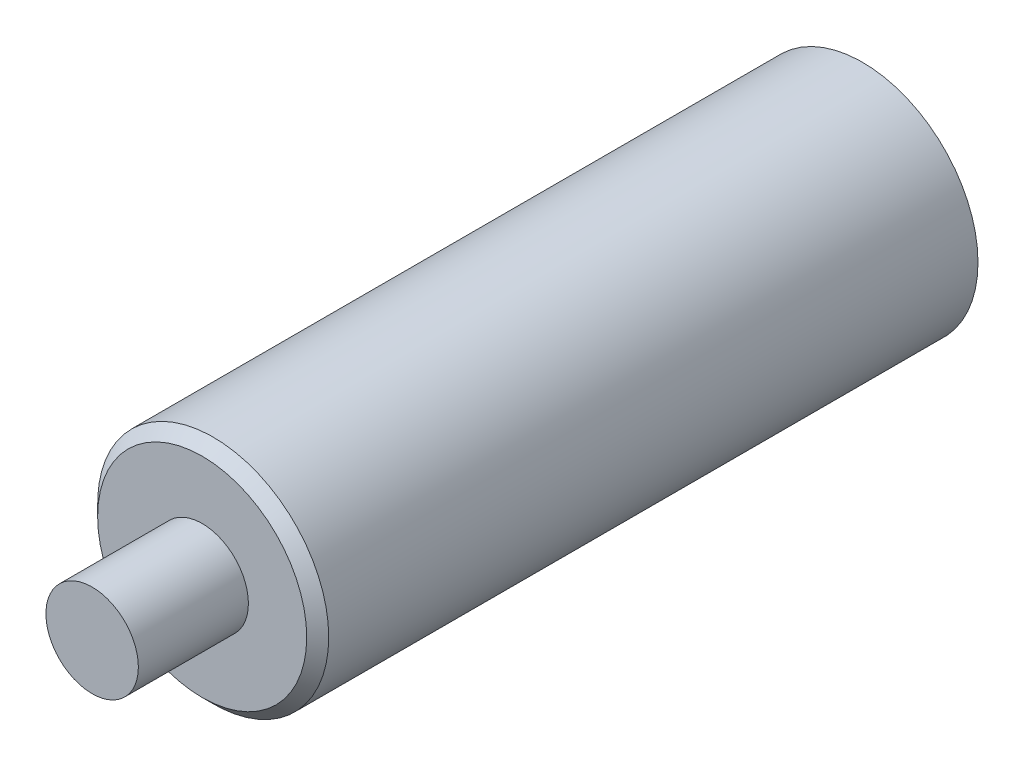
SolidWorks part; units mm, degrees
ref_plane "Front" through (0, 0, 0) normal (0, 0, 1) x (1, 0, 0)
ref_plane "Top" through (0, 0, 0) normal (0, 1, 0) x (1, 0, 0)
ref_plane "Right" through (0, 0, 0) normal (1, 0, 0) x (0, 0, -1)
sketch "Esquisse1" plane through (0, 0, 0) normal (0, 0, 1) x (1, 0, 0)
  circle A0 centre (0, 0) radius 5.25
  dimension "D1" = 10.5
extrude "Boss.-Extru.1" add sketch "Esquisse1" along normal blind 30
chamfer "Chanfrein1" distance 0.5 angle 45 1 edges at (5.25, 0, 30)
sketch "Esquisse2" plane through (0, 0, 0) normal (0, 0, -1) x (-1, 0, 0)
  circle A0 centre (0, 0) radius 1.75
  dimension "D1" = 3.5
extrude "Enlèv. mat.-Extru.1" cut sketch "Esquisse2" against normal blind 15 and the other way through all
sketch "Esquisse4" plane through (0, 0, 30) normal (0, 0, 1) x (1, 0, 0)
  circle A0 centre (0, 0) radius 2.1
  dimension "D1" = 4.2
extrude "Boss.-Extru.2" add sketch "Esquisse4" along normal blind 5
